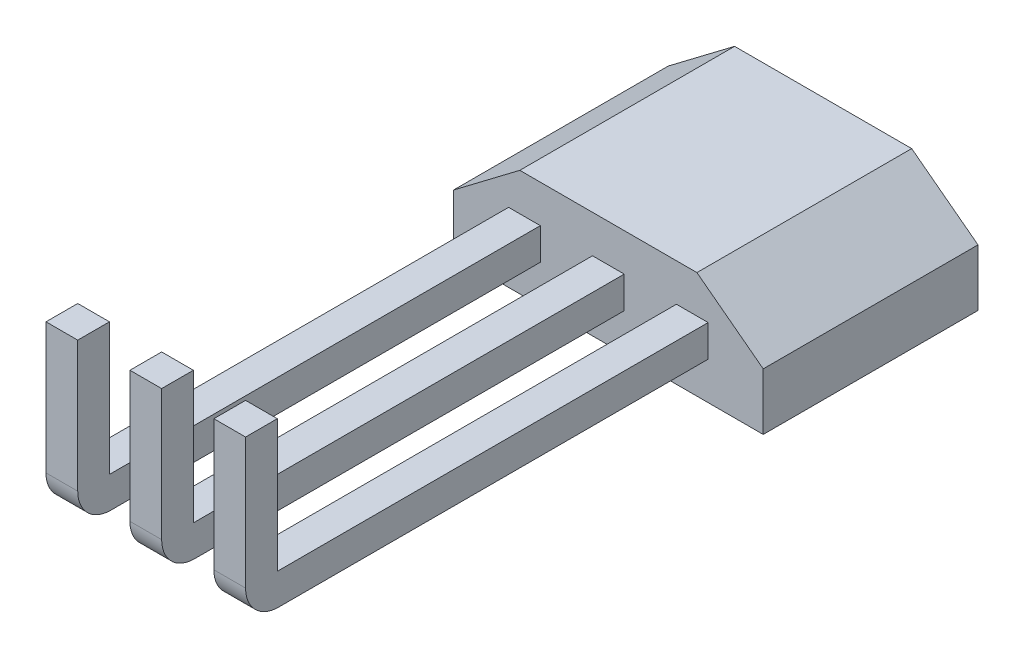
SolidWorks part; units mm, degrees
ref_plane "Alzado" through (0, 0, 0) normal (0, 0, 1) x (1, 0, 0)
ref_plane "Planta" through (0, 0, 0) normal (0, 1, 0) x (1, 0, 0)
ref_plane "Vista lateral" through (0, 0, 0) normal (1, 0, 0) x (0, 0, -1)
sketch "Croquis2" plane through (0, 0, 0) normal (0, 0, 1) x (1, 0, 0)
  line L0 (-2.3434, 0) -> (2.3434, 0)
  line L1 (2.3434, 0) -> (2.3434, 0.86)
  line L5 (-2.3434, 0) -> (-2.3434, 0.86)
  line L6 (0, 0) -> (0, 1.62) construction
  line L7 (-1.34, 1.62) -> (1.34, 1.62)
  line L8 (1.34, 1.62) -> (2.3434, 0.86)
  line L9 (-1.34, 1.62) -> (-2.3434, 0.86)
  point P4 (0, 0)
  point P11 (0, 1.62)
  dimension "D1" = 0.86
  dimension "D2" = 4.6868
  dimension "D3" = 1.62
  dimension "D4" = 2.68
extrude "Saliente-Extruir1" add sketch "Croquis2" along normal blind 3.25
sketch "Croquis3" plane through (0, 0, 3.25) normal (0, 0, 1) x (1, 0, 0)
  line L0 (0, 0) -> (0, 1.62) construction
  line L1 (-2.3434, 0) -> (2.3434, 0) construction
  line L2 (1.34, 1.62) -> (-1.34, 1.62) construction
  line L3 (-2.3434, 0.81) -> (2.3434, 0.81) construction
  line L4 (2.3434, 0) -> (2.3434, 0.86) construction
  line L6 (-0.24, 1.05) -> (0.24, 1.05)
  line L7 (-0.24, 1.05) -> (-0.24, 0.57)
  line L8 (-0.24, 0.57) -> (0.24, 0.57)
  line L9 (0.24, 1.05) -> (0.24, 0.57)
  line L10 (-0.24, 1.05) -> (0.24, 0.57) construction
  line L11 (-0.24, 0.57) -> (0.24, 1.05) construction
  line L12 (1.03, 1.05) -> (1.51, 1.05)
  line L13 (1.03, 1.05) -> (1.03, 0.57)
  line L14 (1.03, 0.57) -> (1.51, 0.57)
  line L15 (1.51, 1.05) -> (1.51, 0.57)
  line L16 (1.03, 1.05) -> (1.51, 0.57) construction
  line L17 (1.03, 0.57) -> (1.51, 1.05) construction
  line L18 (-1.51, 1.05) -> (-1.03, 1.05)
  line L19 (-1.51, 1.05) -> (-1.51, 0.57)
  line L20 (-1.51, 0.57) -> (-1.03, 0.57)
  line L21 (-1.03, 1.05) -> (-1.03, 0.57)
  line L22 (-1.51, 1.05) -> (-1.03, 0.57) construction
  line L23 (-1.51, 0.57) -> (-1.03, 1.05) construction
  point P6 (0, 0.81)
  point P11 (0, 0.81)
  point P16 (1.27, 0.81)
  point P21 (-1.27, 0.81)
  dimension "D1" = 0.48
  dimension "D2" = 1.27
  dimension "D3" = 1.27
extrude "Saliente-Extruir2" add sketch "Croquis3" along normal blind 7
sketch "Croquis4" plane through (0, 1.05, 0) normal (0, 1, 0) x (1, 0, 0)
  line L0 (-1.03, -10.25) -> (-1.03, -3.25) construction
  line L1 (-1.51, -10.25) -> (-1.03, -10.25)
  line L2 (-1.51, -10.25) -> (-1.51, -9.77)
  line L3 (-1.51, -9.77) -> (-1.03, -9.77)
  line L4 (-1.03, -10.25) -> (-1.03, -9.77)
  line L5 (0.24, -10.25) -> (0.24, -3.25) construction
  line L6 (-0.24, -10.25) -> (0.24, -10.25)
  line L7 (-0.24, -10.25) -> (-0.24, -9.77)
  line L8 (-0.24, -9.77) -> (0.24, -9.77)
  line L9 (0.24, -10.25) -> (0.24, -9.77)
  line L10 (1.51, -10.25) -> (1.51, -3.25) construction
  line L11 (1.03, -10.25) -> (1.51, -10.25)
  line L12 (1.03, -10.25) -> (1.03, -9.77)
  line L13 (1.03, -9.77) -> (1.51, -9.77)
  line L14 (1.51, -10.25) -> (1.51, -9.77)
extrude "Saliente-Extruir3" add sketch "Croquis4" along normal blind 2
fillet "Redondeo1" radius 0.5 3 edges at (1.27, 0.57, 10.25) (0, 0.57, 10.25) (-1.27, 0.57, 10.25)
